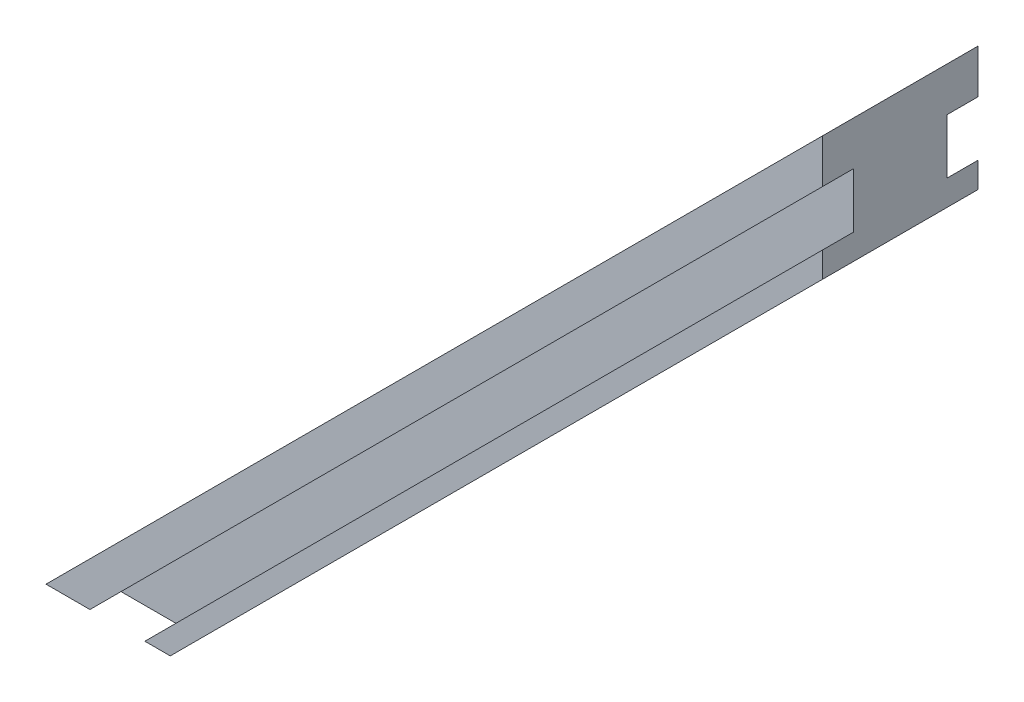
SolidWorks part; units mm, degrees
ref_plane "Front Plane" through (0, 0, 0) normal (0, 0, 1) x (1, 0, 0)
ref_plane "Top Plane" through (0, 0, 0) normal (0, 1, 0) x (1, 0, 0)
ref_plane "Right Plane" through (0, 0, 0) normal (1, 0, 0) x (0, 0, -1)
sketch "Sketch1" plane through (0, 0, 0) normal (0, 0, 1) x (1, 0, 0)
  line L0 (-25, -25) -> (25, 25)
  line L1 (25, 25) -> (25, 17)
  line L2 (-17, -25) -> (25, 17)
  line L6 (-25, -25) -> (-17, -25)
  point P4 (7.5, -7.5)
  point P13 (0, 0)
  dimension "D1" = 45
  dimension "D2" = 8
  dimension "D3" = 50
  dimension "D5" = 70.7107
extrude "Main" add sketch "Sketch1" along normal mid plane 10
sketch "Sketch4" plane through (0, 0, 5) normal (0, 0, 1) x (1, 0, 0)
  line L0 (25, 22.1716) -> (-22.1716, -25)
  line L1 (-22.1716, -25) -> (-18.636, -25)
  line L2 (-18.636, -25) -> (25, 18.636)
  line L3 (25, 18.636) -> (25, 22.1716)
  line L4 (25, 25) -> (-25, -25) construction
  line L5 (-25, -25) -> (-17, -25) construction
  line L6 (25, 17) -> (25, 25) construction
  dimension "D1" = 2.5
  dimension "D2" = 2
  dimension "D3" = 66.7107
  dimension "D4" = 61.7107
extrude "WindowSlot1" cut sketch "Sketch4" against normal blind 2
mirror "Mirror1" about plane through (0, 0, 0) normal (0, 0, 1) of "WindowSlot1"
sketch "Sketch6" plane through (4, -4, 0) normal (-0.7071, 0.7071, 0) x (0, 0, 1)
  circle A0 centre (0, 20) radius 1.25
  dimension "D1" = 2.5
  dimension "D2" = 20
extrude "Cut-Extrude2" cut sketch "Sketch6" along normal blind 5
pattern_linear "LPattern1" count 5 spacing 10 along (-0.7071, -0.7071, 0) of "Cut-Extrude2"
sketch "Sketch7" plane through (0, 0, 0) normal (-0.7071, 0.7071, 0) x (0, 0, 1)
  circle A0 centre (0, 20) radius 3.5
  circle A1 centre (0, 20) radius 1.25 construction
  circle A2 centre (0, -20) radius 3.5
  dimension "D1" = 7
extrude "Cut-Extrude4" cut sketch "Sketch7" against normal blind 1.5
